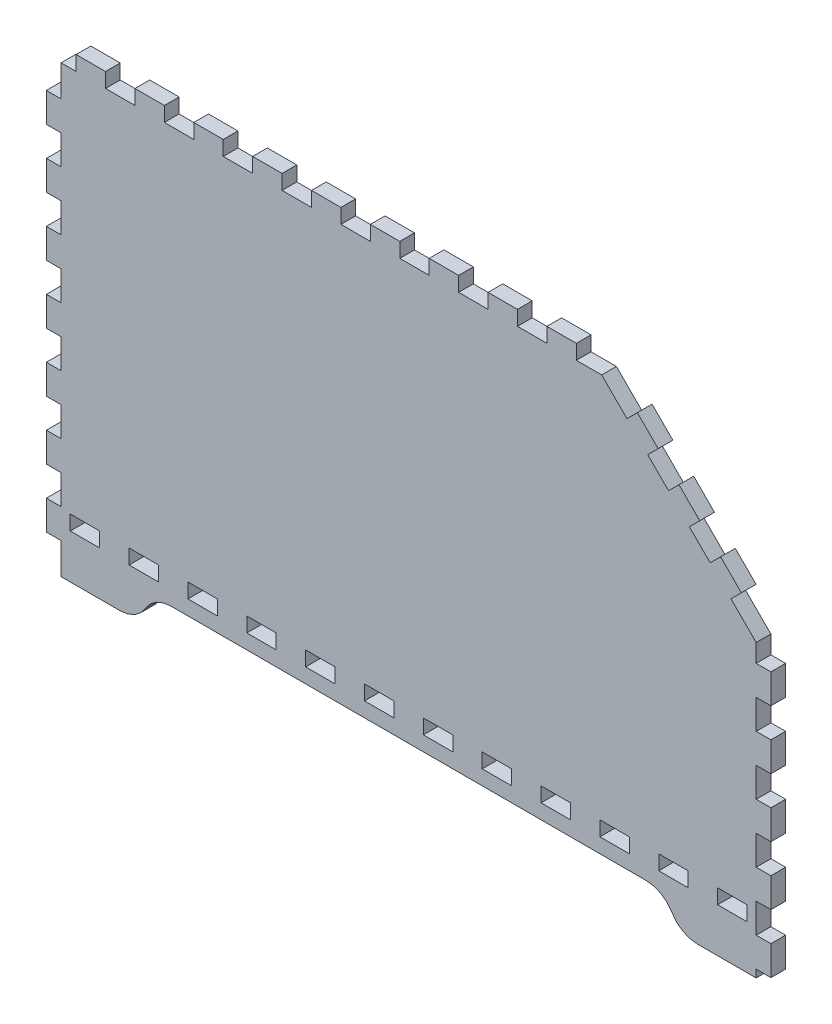
SolidWorks part; units mm, degrees
ref_plane "Front Plane" through (0, 0, 0) normal (0, 0, 1) x (1, 0, 0)
ref_plane "Top Plane" through (0, 0, 0) normal (0, 1, 0) x (1, 0, 0)
ref_plane "Right Plane" through (0, 0, 0) normal (1, 0, 0) x (0, 0, -1)
sketch "Model" plane through (0, 0, 0) normal (0, 0, 1) x (1, 0, 0)
  line L4 (25.385, 40.0054) -> (19.67, 40.0054)
  line L5 (19.67, 40.0054) -> (19.67, 45.7204)
  line L6 (19.67, 45.7204) -> (31.1, 45.7204)
  line L7 (31.1, 45.7204) -> (31.1, 40.0054)
  line L8 (31.1, 40.0054) -> (25.385, 40.0054)
  line L9 (48.245, 40.0054) -> (42.53, 40.0054)
  line L10 (42.53, 40.0054) -> (42.53, 45.7204)
  line L11 (42.53, 45.7204) -> (53.96, 45.7204)
  line L12 (53.96, 45.7204) -> (53.96, 40.0054)
  line L13 (53.96, 40.0054) -> (48.245, 40.0054)
  line L14 (71.105, 40.0054) -> (65.39, 40.0054)
  line L15 (65.39, 40.0054) -> (65.39, 45.7204)
  line L16 (65.39, 45.7204) -> (76.82, 45.7204)
  line L17 (76.82, 45.7204) -> (76.82, 40.0054)
  line L18 (76.82, 40.0054) -> (71.105, 40.0054)
  line L19 (93.9651, 40.0054) -> (88.2501, 40.0054)
  line L20 (88.2501, 40.0054) -> (88.2501, 45.7204)
  line L21 (88.2501, 45.7204) -> (99.6801, 45.7204)
  line L22 (99.6801, 45.7204) -> (99.6801, 40.0054)
  line L23 (99.6801, 40.0054) -> (93.9651, 40.0054)
  line L24 (116.8251, 40.0054) -> (111.1101, 40.0054)
  line L25 (111.1101, 40.0054) -> (111.1101, 45.7204)
  line L26 (111.1101, 45.7204) -> (122.5401, 45.7204)
  line L27 (122.5401, 45.7204) -> (122.5401, 40.0054)
  line L28 (122.5401, 40.0054) -> (116.8251, 40.0054)
  line L29 (139.6851, 40.0054) -> (133.9701, 40.0054)
  line L30 (133.9701, 40.0054) -> (133.9701, 45.7204)
  line L31 (133.9701, 45.7204) -> (145.4001, 45.7204)
  line L32 (145.4001, 45.7204) -> (145.4001, 40.0054)
  line L33 (145.4001, 40.0054) -> (139.6851, 40.0054)
  line L34 (162.5451, 40.0054) -> (156.8301, 40.0054)
  line L35 (156.8301, 40.0054) -> (156.8301, 45.7204)
  line L36 (156.8301, 45.7204) -> (168.2602, 45.7204)
  line L37 (168.2602, 45.7204) -> (168.2602, 40.0054)
  line L38 (168.2602, 40.0054) -> (162.5451, 40.0054)
  line L39 (185.4052, 40.0054) -> (179.6902, 40.0054)
  line L40 (179.6902, 40.0054) -> (179.6902, 45.7204)
  line L41 (179.6902, 45.7204) -> (191.1202, 45.7204)
  line L42 (191.1202, 45.7204) -> (191.1202, 40.0054)
  line L43 (191.1202, 40.0054) -> (185.4052, 40.0054)
  line L44 (208.2652, 40.0054) -> (202.5502, 40.0054)
  line L45 (202.5502, 40.0054) -> (202.5502, 45.7204)
  line L46 (202.5502, 45.7204) -> (213.9802, 45.7204)
  line L47 (213.9802, 45.7204) -> (213.9802, 40.0054)
  line L48 (213.9802, 40.0054) -> (208.2652, 40.0054)
  line L49 (231.1252, 40.0054) -> (225.4102, 40.0054)
  line L50 (225.4102, 40.0054) -> (225.4102, 45.7204)
  line L51 (225.4102, 45.7204) -> (236.8402, 45.7204)
  line L52 (236.8402, 45.7204) -> (236.8402, 40.0054)
  line L53 (236.8402, 40.0054) -> (231.1252, 40.0054)
  line L54 (253.9853, 40.0054) -> (248.2702, 40.0054)
  line L55 (248.2702, 40.0054) -> (248.2702, 45.7204)
  line L56 (248.2702, 45.7204) -> (259.7003, 45.7204)
  line L57 (259.7003, 45.7204) -> (259.7003, 40.0054)
  line L58 (259.7003, 40.0054) -> (253.9853, 40.0054)
  line L59 (276.8449, 40.0054) -> (271.1303, 40.0054)
  line L60 (271.1303, 40.0054) -> (271.1303, 45.7204)
  line L61 (271.1303, 45.7204) -> (282.5599, 45.7204)
  line L62 (282.5599, 45.7204) -> (282.5599, 40.0054)
  line L63 (282.5599, 40.0054) -> (276.8449, 40.0054)
  line L64 (16.115, 22.8602) -> (38.975, 22.8602)
  line L65 (38.975, 22.8602) -> (41.933, 23.2496)
  line L66 (41.933, 23.2496) -> (44.69, 24.3912)
  line L67 (44.69, 24.3912) -> (47.0573, 26.208)
  line L68 (47.0573, 26.208) -> (48.874, 28.5752)
  line L69 (48.874, 28.5752) -> (50.6903, 30.9425)
  line L70 (50.6903, 30.9425) -> (53.0572, 32.7593)
  line L71 (53.0572, 32.7593) -> (55.8141, 33.9009)
  line L72 (55.8141, 33.9009) -> (58.7722, 34.2903)
  line L73 (58.7722, 34.2903) -> (243.4581, 34.2903)
  line L74 (243.4581, 34.2903) -> (246.416, 33.9009)
  line L75 (246.416, 33.9009) -> (249.1731, 32.7593)
  line L76 (249.1731, 32.7593) -> (251.5398, 30.9425)
  line L77 (251.5398, 30.9425) -> (253.356, 28.5752)
  line L78 (253.356, 28.5752) -> (255.1729, 26.208)
  line L79 (255.1729, 26.208) -> (257.5403, 24.3912)
  line L80 (257.5403, 24.3912) -> (260.2972, 23.2496)
  line L81 (260.2972, 23.2496) -> (263.2553, 22.8602)
  line L82 (263.2553, 22.8602) -> (286.1149, 22.8602)
  line L83 (286.1149, 22.8602) -> (286.1149, 25.8342)
  line L84 (286.1149, 25.8342) -> (291.8299, 25.8342)
  line L85 (291.8299, 25.8342) -> (291.8299, 37.2643)
  line L86 (291.8299, 37.2643) -> (286.1149, 37.2643)
  line L87 (286.1149, 37.2643) -> (286.1149, 48.6943)
  line L88 (286.1149, 48.6943) -> (291.8299, 48.6943)
  line L89 (291.8299, 48.6943) -> (291.8299, 60.1243)
  line L90 (291.8299, 60.1243) -> (286.1149, 60.1243)
  line L91 (286.1149, 60.1243) -> (286.1149, 71.5543)
  line L92 (286.1149, 71.5543) -> (291.8299, 71.5543)
  line L93 (291.8299, 71.5543) -> (291.8299, 82.9843)
  line L94 (291.8299, 82.9843) -> (286.1149, 82.9843)
  line L95 (286.1149, 82.9843) -> (286.1149, 94.4144)
  line L96 (286.1149, 94.4144) -> (291.8299, 94.4144)
  line L97 (291.8299, 94.4144) -> (291.8299, 105.8444)
  line L98 (291.8299, 105.8444) -> (286.1149, 105.8444)
  line L99 (286.1149, 105.8444) -> (286.1149, 117.2744)
  line L100 (286.1149, 117.2744) -> (291.8299, 117.2744)
  line L101 (291.8299, 117.2744) -> (291.8299, 128.7044)
  line L102 (291.8299, 128.7044) -> (286.1149, 128.7044)
  line L103 (286.1149, 128.7044) -> (286.1149, 131.6794)
  line L104 (286.1149, 131.6794) -> (286.1149, 135.7202)
  line L105 (286.1149, 135.7202) -> (276.3212, 145.5142)
  line L106 (276.3212, 145.5142) -> (280.362, 149.5564)
  line L107 (280.362, 149.5564) -> (272.279, 157.6384)
  line L108 (272.279, 157.6384) -> (268.2382, 153.5972)
  line L109 (268.2382, 153.5972) -> (260.1559, 161.6792)
  line L110 (260.1559, 161.6792) -> (264.1971, 165.7203)
  line L111 (264.1971, 165.7203) -> (256.1151, 173.8022)
  line L112 (256.1151, 173.8022) -> (252.074, 169.7615)
  line L113 (252.074, 169.7615) -> (243.9921, 177.8434)
  line L114 (243.9921, 177.8434) -> (248.0332, 181.8842)
  line L115 (248.0332, 181.8842) -> (239.9513, 189.9672)
  line L116 (239.9513, 189.9672) -> (235.909, 185.9264)
  line L117 (235.909, 185.9264) -> (226.115, 195.7205)
  line L118 (226.115, 195.7205) -> (222.0742, 195.7205)
  line L119 (222.0742, 195.7205) -> (216.249, 195.7205)
  line L120 (216.249, 195.7205) -> (216.249, 201.4355)
  line L121 (216.249, 201.4355) -> (204.819, 201.4355)
  line L122 (204.819, 201.4355) -> (204.819, 195.7205)
  line L123 (204.819, 195.7205) -> (193.389, 195.7205)
  line L124 (193.389, 195.7205) -> (193.389, 201.4355)
  line L125 (193.389, 201.4355) -> (181.9589, 201.4355)
  line L126 (181.9589, 201.4355) -> (181.9589, 195.7205)
  line L127 (181.9589, 195.7205) -> (170.5289, 195.7205)
  line L128 (170.5289, 195.7205) -> (170.5289, 201.4355)
  line L129 (170.5289, 201.4355) -> (159.0989, 201.4355)
  line L130 (159.0989, 201.4355) -> (159.0989, 195.7205)
  line L131 (159.0989, 195.7205) -> (147.6689, 195.7205)
  line L132 (147.6689, 195.7205) -> (147.6689, 201.4355)
  line L133 (147.6689, 201.4355) -> (136.2389, 201.4355)
  line L134 (136.2389, 201.4355) -> (136.2389, 195.7205)
  line L135 (136.2389, 195.7205) -> (124.8089, 195.7205)
  line L136 (124.8089, 195.7205) -> (124.8089, 201.4355)
  line L137 (124.8089, 201.4355) -> (113.3789, 201.4355)
  line L138 (113.3789, 201.4355) -> (113.3789, 195.7205)
  line L139 (113.3789, 195.7205) -> (101.9492, 195.7205)
  line L140 (101.9492, 195.7205) -> (101.9492, 201.4355)
  line L141 (101.9492, 201.4355) -> (90.5192, 201.4355)
  line L142 (90.5192, 201.4355) -> (90.5192, 195.7205)
  line L143 (90.5192, 195.7205) -> (79.0892, 195.7205)
  line L144 (79.0892, 195.7205) -> (79.0892, 201.4355)
  line L145 (79.0892, 201.4355) -> (67.6592, 201.4355)
  line L146 (67.6592, 201.4355) -> (67.6592, 195.7205)
  line L147 (67.6592, 195.7205) -> (56.2292, 195.7205)
  line L148 (56.2292, 195.7205) -> (56.2292, 201.4355)
  line L149 (56.2292, 201.4355) -> (44.7991, 201.4355)
  line L150 (44.7991, 201.4355) -> (44.7991, 195.7205)
  line L151 (44.7991, 195.7205) -> (33.369, 195.7205)
  line L152 (33.369, 195.7205) -> (33.369, 201.4355)
  line L153 (33.369, 201.4355) -> (21.939, 201.4355)
  line L154 (21.939, 201.4355) -> (21.939, 195.7205)
  line L155 (21.939, 195.7205) -> (16.115, 195.7205)
  line L156 (16.115, 195.7205) -> (16.115, 183.5853)
  line L157 (16.115, 183.5853) -> (10.4, 183.5853)
  line L158 (10.4, 183.5853) -> (10.4, 172.1553)
  line L159 (10.4, 172.1553) -> (16.115, 172.1553)
  line L160 (16.115, 172.1553) -> (16.115, 160.7253)
  line L161 (16.115, 160.7253) -> (10.4, 160.7253)
  line L162 (10.4, 160.7253) -> (10.4, 149.2953)
  line L163 (10.4, 149.2953) -> (16.115, 149.2953)
  line L164 (16.115, 149.2953) -> (16.115, 137.8653)
  line L165 (16.115, 137.8653) -> (10.4, 137.8653)
  line L166 (10.4, 137.8653) -> (10.4, 126.4353)
  line L167 (10.4, 126.4353) -> (16.115, 126.4353)
  line L168 (16.115, 126.4353) -> (16.115, 115.0052)
  line L169 (16.115, 115.0052) -> (10.4, 115.0052)
  line L170 (10.4, 115.0052) -> (10.4, 103.5752)
  line L171 (10.4, 103.5752) -> (16.115, 103.5752)
  line L172 (16.115, 103.5752) -> (16.115, 92.1452)
  line L173 (16.115, 92.1452) -> (10.4, 92.1452)
  line L174 (10.4, 92.1452) -> (10.4, 80.7152)
  line L175 (10.4, 80.7152) -> (16.115, 80.7152)
  line L176 (16.115, 80.7152) -> (16.115, 69.2852)
  line L177 (16.115, 69.2852) -> (10.4, 69.2852)
  line L178 (10.4, 69.2852) -> (10.4, 57.8552)
  line L179 (10.4, 57.8552) -> (16.115, 57.8552)
  line L180 (16.115, 57.8552) -> (16.115, 46.4252)
  line L181 (16.115, 46.4252) -> (10.4, 46.4252)
  line L182 (10.4, 46.4252) -> (10.4, 34.9953)
  line L183 (10.4, 34.9953) -> (16.115, 34.9953)
  line L184 (16.115, 34.9953) -> (16.115, 22.8602)
extrude "Boss-Extrude1" add sketch "Model" along normal blind 5.715
